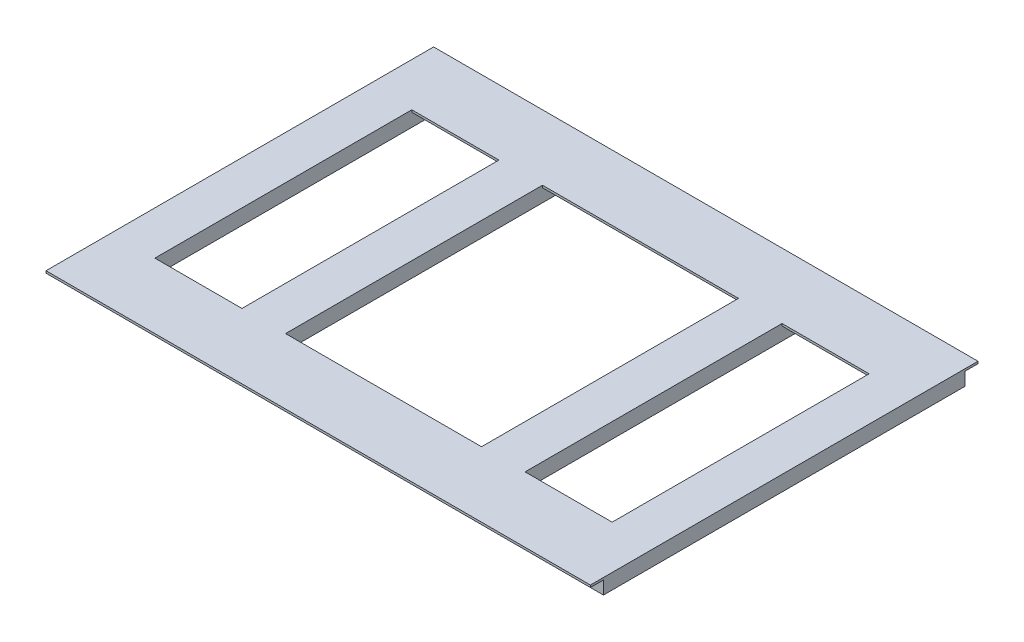
SolidWorks part; units mm, degrees
material "6061 Alloy"
ref_plane "Front Plane" through (0, 0, 0) normal (0, 0, 1) x (1, 0, 0)
ref_plane "Top Plane" through (0, 0, 0) normal (0, 1, 0) x (1, 0, 0)
ref_plane "Right Plane" through (0, 0, 0) normal (1, 0, 0) x (0, 0, -1)
sketch "Sketch1" plane through (0, 0, 0) normal (0, 1, 0) x (1, 0, 0)
  line L1 (0, 0) -> (-2500, 0)
  line L2 (0, 0) -> (0, 300)
  line L3 (0, 300) -> (-2500, 300)
  line L4 (-2500, 0) -> (-2500, 300)
  dimension "D1" = 300
  dimension "D2" = 2500
extrude "Extrude1" add sketch "Sketch1" along normal blind 10
sketch "Sketch2" plane through (0, 0, 0) normal (0, -1, 0) x (1, 0, 0)
  line L0 (0, 0) -> (0, -300) construction
  line L1 (0, -60) -> (-2500, -60)
  line L2 (0, -60) -> (0, -80)
  line L3 (0, -80) -> (-2500, -80)
  line L4 (-2500, -60) -> (-2500, -80)
  line L5 (-2500, -300) -> (-2500, 0) construction
  line L6 (0, -300) -> (-2500, -300) construction
  line L7 (0, -220) -> (-2500, -220)
  line L8 (0, -220) -> (0, -240)
  line L9 (0, -240) -> (-2500, -240)
  line L10 (-2500, -220) -> (-2500, -240)
  line L11 (-2500, 0) -> (0, 0) construction
  dimension "D1" = 60
  dimension "D2" = 20
  dimension "D3" = 60
  dimension "D4" = 20
extrude "Extrude2" add sketch "Sketch2" along normal blind 60
sketch "Sketch3" plane through (0, 0, 0) normal (0, -1, 0) x (1, 0, 0)
  line L0 (0, -300) -> (-2500, -300) construction
  line L1 (0, -300) -> (-200, -300)
  line L2 (0, -300) -> (0, -890)
  line L3 (0, -890) -> (-200, -890)
  line L4 (-200, -300) -> (-200, -890)
  line L5 (-600, -300) -> (-800, -300)
  line L6 (-600, -300) -> (-600, -890)
  line L7 (-600, -890) -> (-800, -890)
  line L8 (-800, -300) -> (-800, -890)
  line L10 (-1700, -300) -> (-1900, -300)
  line L11 (-1700, -300) -> (-1700, -890)
  line L12 (-1700, -890) -> (-1900, -890)
  line L13 (-1900, -300) -> (-1900, -890)
  line L14 (-2300, -300) -> (-2500, -300)
  line L15 (-2300, -300) -> (-2300, -890)
  line L16 (-2300, -890) -> (-2500, -890)
  line L17 (-2500, -300) -> (-2500, -890)
  dimension "D1" = 200
  dimension "D2" = 200
  dimension "D3" = 200
  dimension "D4" = 200
  dimension "D5" = 400
  dimension "D6" = 400
  dimension "D7" = 590
  dimension "D8" = 590
  dimension "D9" = 590
  dimension "D10" = 590
extrude "Extrude3" add sketch "Sketch3" against normal blind 10
sketch "Sketch5" plane through (0, 0, 0) normal (0, -1, 0) x (1, 0, 0)
  line L0 (-2500, -240) -> (0, -240) construction
  line L1 (-2500, -890) -> (-2480, -890)
  line L2 (-2500, -890) -> (-2500, -80)
  line L3 (-2500, -80) -> (-2480, -80)
  line L4 (-2480, -890) -> (-2480, -80)
  line L5 (-1700, -890) -> (-1700, -300) construction
  line L6 (-2300, -890) -> (-2320, -890)
  line L7 (-2300, -890) -> (-2300, -240)
  line L8 (-2300, -240) -> (-2320, -240)
  line L9 (-2320, -890) -> (-2320, -240)
  line L10 (-1900, -890) -> (-1880, -890)
  line L11 (-1900, -890) -> (-1900, -240)
  line L12 (-1900, -240) -> (-1880, -240)
  line L13 (-1880, -890) -> (-1880, -240)
  line L14 (-1700, -890) -> (-1720, -890)
  line L15 (-1700, -890) -> (-1700, -240)
  line L16 (-1700, -240) -> (-1720, -240)
  line L17 (-1720, -890) -> (-1720, -240)
  line L18 (-1900, -890) -> (-1700, -890) construction
  line L19 (-2500, -240) -> (0, -240) construction
  line L20 (-2500, -80) -> (0, -80) construction
  line L21 (-800, -890) -> (-780, -890)
  line L22 (-800, -890) -> (-800, -240)
  line L23 (-800, -240) -> (-780, -240)
  line L24 (-780, -890) -> (-780, -240)
  line L25 (-600, -890) -> (-620, -890)
  line L26 (-600, -890) -> (-600, -240)
  line L27 (-600, -240) -> (-620, -240)
  line L28 (-620, -890) -> (-620, -240)
  line L29 (-200, -890) -> (-180, -890)
  line L30 (-200, -890) -> (-200, -240)
  line L31 (-200, -240) -> (-180, -240)
  line L32 (-180, -890) -> (-180, -240)
  line L33 (0, -890) -> (-20, -890)
  line L34 (0, -890) -> (0, -80)
  line L35 (0, -80) -> (-20, -80)
  line L36 (-20, -890) -> (-20, -80)
  dimension "D1" = 20
  dimension "D2" = 20
  dimension "D3" = 20
  dimension "D4" = 20
  dimension "D5" = 20
  dimension "D6" = 20
  dimension "D7" = 20
  dimension "D8" = 20
extrude "Extrude7" add sketch "Sketch5" along normal blind 60
mirror "Mirror2"
